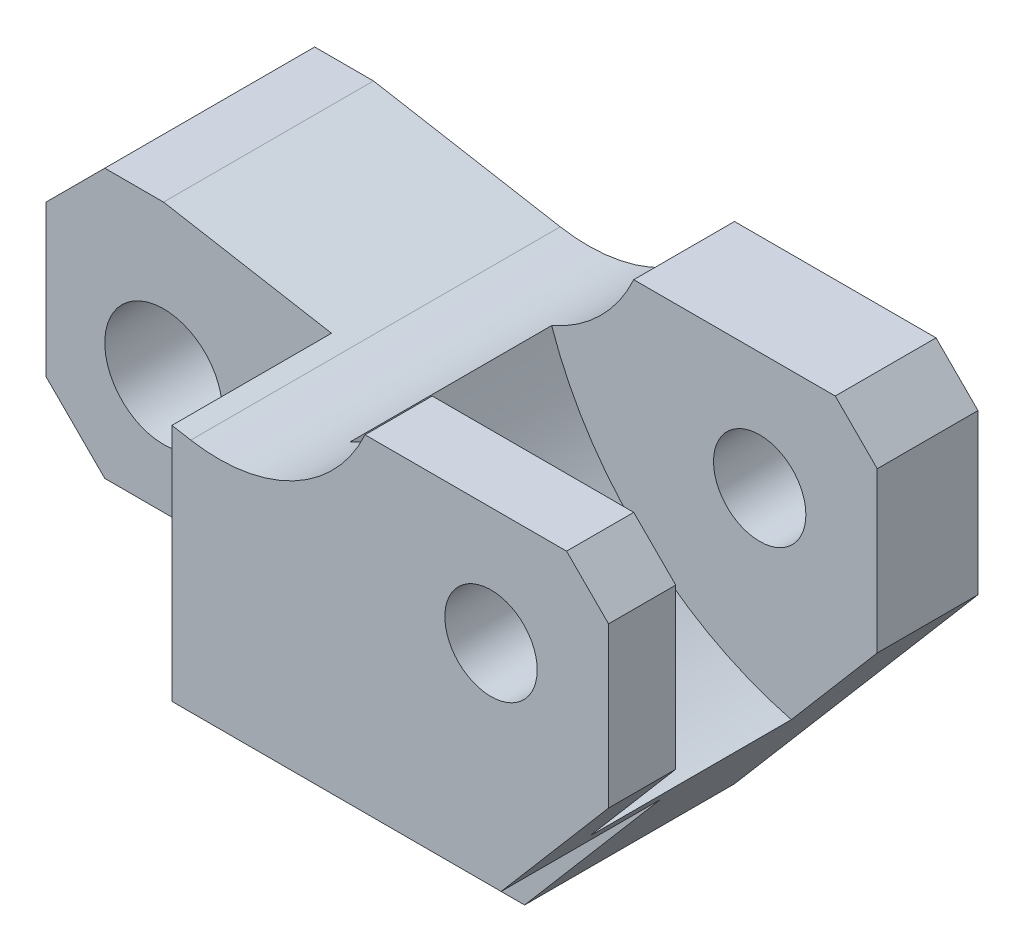
SolidWorks part; units mm, degrees
material "AISI 1020"
ref_plane "Plan de face" through (0, 0, 0) normal (0, 0, 1) x (1, 0, 0)
ref_plane "Plan de dessus" through (0, 0, 0) normal (0, 1, 0) x (1, 0, 0)
ref_plane "Plan de droite" through (0, 0, 0) normal (1, 0, 0) x (0, 0, -1)
sketch "Esquisse2" plane through (0, 0, 0) normal (0, 0, 1) x (1, 0, 0)
  line L0 (51.297, -19) -> (57, -19)
  line L1 (57, -19) -> (86, 15)
  line L2 (86, 15) -> (86, 34)
  line L3 (81, 39) -> (57, 39)
  line L4 (36.2464, 28.0774) -> (14, 32)
  line L5 (14, 32) -> (7, 32)
  line L6 (0, 25) -> (0, 7)
  line L7 (7, 0) -> (39.5755, 0)
  line L8 (7, 32) -> (0, 25)
  line L9 (0, 7) -> (7, 0)
  line L10 (86, 34) -> (81, 39)
  arc A0 (57, 39) -> (36.2464, 28.0774) centre (39.5718, 46.9367) cw
  arc A1 (39.5755, 0) -> (44.5212, -4.2647) centre (39.5755, -5) cw
  arc A2 (44.5212, -4.2647) -> (51.297, -19) centre (73.2059, 0) ccw
  circle A3 centre (14, 14) radius 7
  point P4 (86, 39)
  point P9 (0, 32)
  point P10 (0, 0)
  dimension "D3" = 29
  dimension "D7" = 19.1503
  dimension "D10" = 5
  dimension "D13" = 14
  dimension "D1" = 86
  dimension "D2" = 58
  dimension "D4" = 29
  dimension "D5" = 24
  dimension "D6" = 14
  dimension "D8" = 10
  dimension "D9" = 32
  dimension "D11" = 14
  dimension "D12" = 14
  dimension "D14" = 19
  dimension "D15" = 29
  dimension "D16" = 19
  dimension "D17" = 7
  dimension "D18" = 45
  dimension "D19" = 7
  dimension "D20" = 45
  dimension "D21" = 5
  dimension "D22" = 45
extrude "Boss.-Extru.2" add sketch "Esquisse2" along normal mid plane 44
sketch "Esquisse4" plane through (0, 0, 22) normal (0, 0, 1) x (1, 0, 0)
  line L0 (34, 32) -> (0, 32)
  line L1 (0, 32) -> (0, -19)
  line L2 (0, -19) -> (86, -19)
  line L3 (86, -19) -> (86, 0)
  line L4 (86, 0) -> (34, 0)
  line L5 (34, 0) -> (34, 32)
  line L6 (14, 32) -> (7, 32) construction
  line L7 (0, 25) -> (0, 7) construction
  line L8 (51.297, -19) -> (57, -19) construction
  line L9 (86, 15) -> (86, 34) construction
  line L10 (7, 0) -> (39.5755, 0) construction
  dimension "D1" = 52
extrude "Enlèv. mat.-Extru.1" cut sketch "Esquisse4" against normal blind 19
sketch "Esquisse5" plane through (0, 0, 22) normal (0, 0, 1) x (1, 0, 0)
  line L0 (86, 15) -> (86, 34) construction
  line L1 (81, 39) -> (57, 39) construction
  circle A0 centre (72, 25) radius 5.5
  point P4 (86, 24.5)
  dimension "D1" = 11
  dimension "D2" = 14
  dimension "D3" = 14
extrude "Enlèv. mat.-Extru.2" cut sketch "Esquisse5" against normal through all
sketch "Esquisse14" plane through (0, 0, -22) normal (0, 0, -1) x (-1, 0, 0)
  line L0 (-73.2059, 0) -> (-86, 15) construction
  line L1 (-86, 15) -> (-86, 34) construction
  line L2 (-81, 39) -> (-57, 39) construction
  line L3 (-86, 34) -> (-81, 39) construction
  line L4 (-75.7647, 3) -> (-86, 15)
  line L5 (-86, 15) -> (-86, 34)
  line L6 (-86, 34) -> (-81, 39)
  line L7 (-81, 39) -> (-57, 39)
  arc A0 (-75.7647, 3) -> (-47.2241, 29.3817) centre (-86, 42.7019) ccw
  arc A1 (-57, 39) -> (-36.2464, 28.0774) centre (-39.5718, 46.9367) ccw construction
  arc A2 (-57, 39) -> (-47.2241, 29.3817) centre (-39.5718, 46.9367) ccw
  point P10 (0, 0)
  dimension "D1" = 41
  dimension "D2" = 36
extrude "Enlèv. mat.-Extru.3" cut sketch "Esquisse14" against normal blind 24 from offset 12
equation "\"A\" = 86"
equation "\"B\" = 58"
equation "\"C\" = 44"
